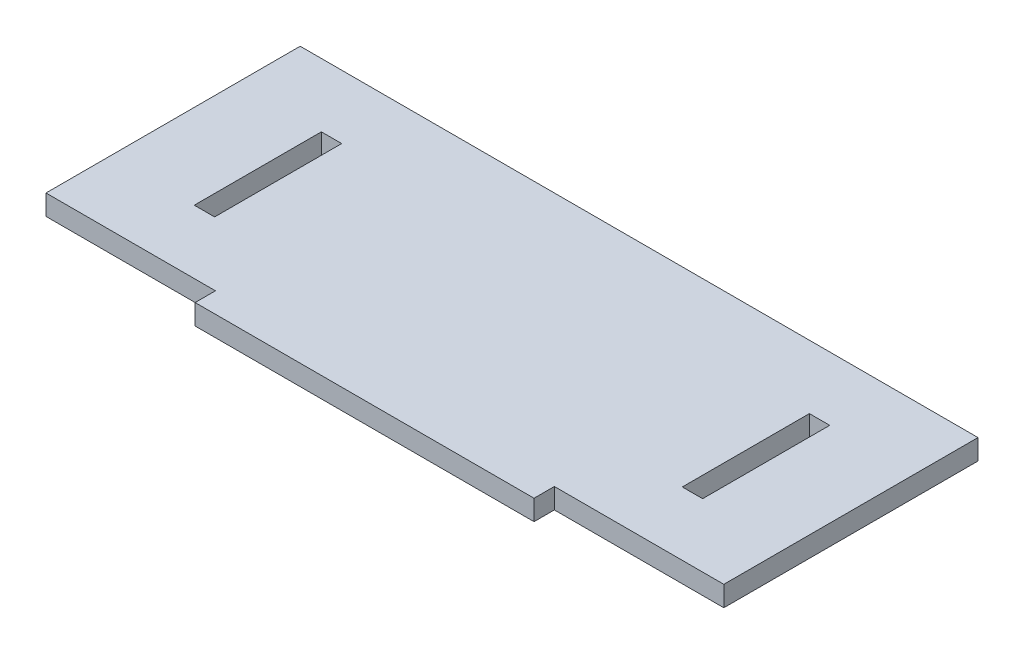
SolidWorks part; units mm, degrees
ref_plane "Front Plane" through (0, 0, 0) normal (0, 0, 1) x (1, 0, 0)
ref_plane "Top Plane" through (0, 0, 0) normal (0, 1, 0) x (1, 0, 0)
ref_plane "Right Plane" through (0, 0, 0) normal (1, 0, 0) x (0, 0, -1)
sketch "Sketch1" plane through (0, 0, 0) normal (0, 1, 0) x (1, 0, 0)
  line L1 (-200, 75) -> (200, 75)
  line L2 (-200, 75) -> (-200, -75)
  line L3 (-200, -75) -> (200, -75)
  line L4 (200, 75) -> (200, -75)
  line L5 (-200, 75) -> (200, -75) construction
  line L6 (-200, -75) -> (200, 75) construction
  line L7 (-100, -63) -> (100, -63)
  line L8 (-100, -63) -> (-100, -87)
  line L9 (-100, -87) -> (100, -87)
  line L10 (100, -63) -> (100, -87)
  line L11 (-100, -63) -> (100, -87) construction
  line L12 (-100, -87) -> (100, -63) construction
  point P0 (0, 0)
  point P5 (0, -75)
  dimension "D1" = 400
  dimension "D2" = 200
  dimension "D3" = 24
  dimension "D4" = 150
extrude "Boss-Extrude1" add sketch "Sketch1" along normal blind 12 contours L7 L10 L3 L4 L1 L2 L8 | L10 L3 L8 L9 | L10 L7 L8 L3
sketch "Sketch3" plane through (0, 12, 0) normal (0, 1, 0) x (1, 0, 0)
  line L0 (-6.6, 0) -> (6.6, 0) construction
  line L1 (-150, -37.5) -> (-138, -37.5)
  line L2 (-150, -37.5) -> (-150, 37.5)
  line L3 (-150, 37.5) -> (-138, 37.5)
  line L4 (-138, -37.5) -> (-138, 37.5)
  line L5 (-150, -37.5) -> (-138, 37.5) construction
  line L6 (-150, 37.5) -> (-138, -37.5) construction
  line L7 (-200, 75) -> (-200, -75) construction
  point P0 (-144, 0)
  dimension "D1" = 75
  dimension "D2" = 12
  dimension "D3" = 50
extrude "Cut-Extrude1" cut sketch "Sketch3" against normal up to surface (12 mm away) contours L2 L3 L4 L1 up to face at (0, 0, 40.5)
mirror "Mirror1" about plane through (0, 0, 0) normal (1, 0, 0) of "Cut-Extrude1"
